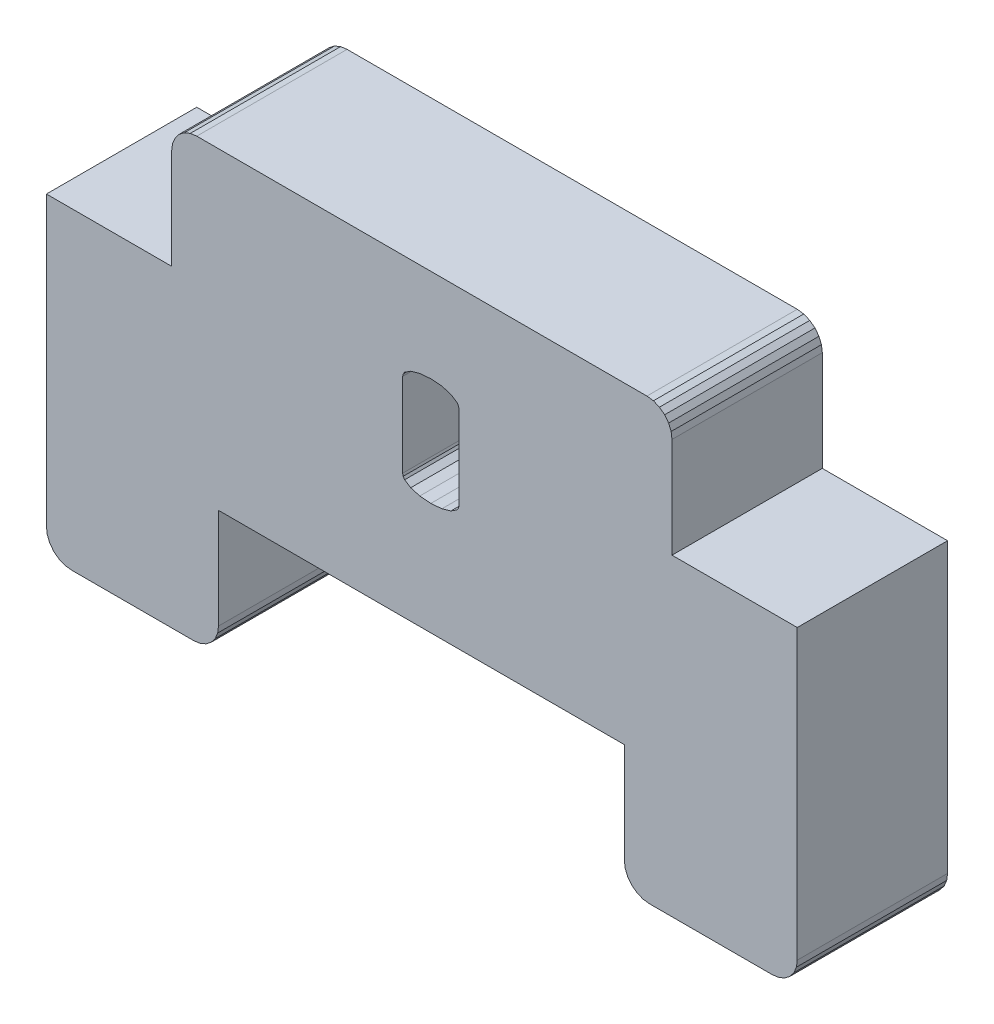
SolidWorks part; units mm, degrees
material "Maple"
ref_plane "Front Plane" through (0, 0, 0) normal (0, 0, 1) x (1, 0, 0)
ref_plane "Top Plane" through (0, 0, 0) normal (0, 1, 0) x (1, 0, 0)
ref_plane "Right Plane" through (0, 0, 0) normal (1, 0, 0) x (0, 0, -1)
sketch "Sketch1" plane through (0, 0, 0) normal (0, 0, 1) x (1, 0, 0)
  line L367 (-477.0213, -244.8724) -> (-477.2801, -244.9065)
  line L368 (-482.6801, -244.7725) -> (-482.439, -244.8724)
  line L369 (-482.8873, -244.6136) -> (-482.6801, -244.7725)
  line L370 (-483.0462, -244.4065) -> (-482.8873, -244.6136)
  line L371 (-499.3801, -243.9065) -> (-499.3801, -239.9065)
  line L372 (-476.2801, -243.9065) -> (-476.2801, -232.4065)
  line L373 (-483.1801, -243.9065) -> (-483.1461, -244.1653)
  line L374 (-476.3142, -244.1653) -> (-476.4141, -244.4065)
  line L375 (-476.4141, -244.4065) -> (-476.573, -244.6136)
  line L376 (-483.1801, -239.9065) -> (-483.1801, -243.9065)
  line L377 (-499.3801, -239.9065) -> (-483.1801, -239.9065)
  line L378 (-501.1146, -227.9065) -> (-500.9557, -227.6993)
  line L379 (-476.573, -244.6136) -> (-476.7801, -244.7725)
  line L380 (-481.7801, -227.5404) -> (-482.0213, -227.4405)
  line L381 (-482.439, -244.8724) -> (-482.1801, -244.9065)
  line L382 (-505.2486, -244.9065) -> (-505.5074, -244.8724)
  line L383 (-500.1213, -244.8724) -> (-500.3801, -244.9065)
  line L384 (-500.5074, -227.4405) -> (-500.2486, -227.4065)
  line L385 (-500.2486, -227.4065) -> (-482.2801, -227.4065)
  line L386 (-476.7801, -244.7725) -> (-477.0213, -244.8724)
  line L387 (-506.2486, -232.4065) -> (-506.2486, -243.9065)
  line L388 (-501.2486, -232.4065) -> (-506.2486, -232.4065)
  line L389 (-500.7486, -227.5404) -> (-500.5074, -227.4405)
  line L390 (-500.9557, -227.6993) -> (-500.7486, -227.5404)
  line L391 (-501.2145, -228.1476) -> (-501.1146, -227.9065)
  line L392 (-501.2486, -228.4065) -> (-501.2145, -228.1476)
  line L393 (-501.2486, -232.4065) -> (-501.2486, -228.4065)
  line L394 (-506.2145, -244.1653) -> (-506.2486, -243.9065)
  line L395 (-506.1146, -244.4065) -> (-506.2145, -244.1653)
  line L396 (-505.9557, -244.6136) -> (-506.1146, -244.4065)
  line L397 (-505.7486, -244.7725) -> (-505.9557, -244.6136)
  line L398 (-505.5074, -244.8724) -> (-505.7486, -244.7725)
  line L399 (-505.2486, -244.9065) -> (-500.3801, -244.9065)
  line L400 (-499.8801, -244.7725) -> (-500.1213, -244.8724)
  line L401 (-499.673, -244.6136) -> (-499.8801, -244.7725)
  line L402 (-499.5141, -244.4065) -> (-499.673, -244.6136)
  line L403 (-499.4142, -244.1653) -> (-499.5141, -244.4065)
  line L404 (-499.3801, -243.9065) -> (-499.4142, -244.1653)
  line L405 (-483.1461, -244.1653) -> (-483.0462, -244.4065)
  line L406 (-482.1801, -244.9065) -> (-477.2801, -244.9065)
  line L407 (-476.2801, -243.9065) -> (-476.3142, -244.1653)
  line L408 (-481.2801, -232.4065) -> (-476.2801, -232.4065)
  line L409 (-481.2801, -228.4065) -> (-481.2801, -232.4065)
  line L410 (-481.2801, -228.4065) -> (-481.3142, -228.1476)
  line L411 (-481.3142, -228.1476) -> (-481.4141, -227.9065)
  line L412 (-481.4141, -227.9065) -> (-481.573, -227.6993)
  line L413 (-481.573, -227.6993) -> (-481.7801, -227.5404)
  line L414 (-482.0213, -227.4405) -> (-482.2801, -227.4065)
  line L8617 (-492.0299, -234.9492) -> (-492.0098, -235.0454)
  line L8618 (-492.0098, -235.0454) -> (-491.9495, -235.1342)
  line L8619 (-491.9495, -235.1342) -> (-491.7083, -235.2895)
  line L8620 (-491.7083, -235.2895) -> (-491.3469, -235.3948)
  line L8621 (-491.3469, -235.3948) -> (-490.906, -235.43)
  line L8622 (-490.906, -235.43) -> (-490.465, -235.3948)
  line L8623 (-490.465, -235.3948) -> (-490.1036, -235.2895)
  line L8624 (-490.1036, -235.2895) -> (-489.8624, -235.1342)
  line L8625 (-489.8624, -235.1342) -> (-489.8021, -235.0454)
  line L8626 (-489.8021, -235.0454) -> (-489.7821, -234.9492)
  line L8627 (-489.7821, -234.9492) -> (-489.7821, -231.6024)
  line L8628 (-489.7821, -231.6024) -> (-489.8021, -231.5063)
  line L8629 (-489.8021, -231.5063) -> (-489.8624, -231.4175)
  line L8630 (-489.8624, -231.4175) -> (-490.1036, -231.2622)
  line L8631 (-490.1036, -231.2622) -> (-490.465, -231.1568)
  line L8632 (-490.465, -231.1568) -> (-490.906, -231.1216)
  line L8633 (-490.906, -231.1216) -> (-491.3469, -231.1568)
  line L8634 (-491.3469, -231.1568) -> (-491.7083, -231.2622)
  line L8635 (-491.7083, -231.2622) -> (-491.9495, -231.4175)
  line L8636 (-491.9495, -231.4175) -> (-492.0098, -231.5063)
  line L8637 (-492.0098, -231.5063) -> (-492.0299, -231.6024)
  line L8638 (-492.0299, -231.6024) -> (-492.0299, -234.9492)
  line L8639 (-489.7821, -234.9492) -> (-489.8021, -235.0454)
  line L8640 (-489.8021, -235.0454) -> (-489.8624, -235.1342)
  line L8641 (-489.8624, -235.1342) -> (-490.1036, -235.2895)
  line L8642 (-490.1036, -235.2895) -> (-490.465, -235.3948)
  line L8643 (-490.465, -235.3948) -> (-490.906, -235.43)
  line L8644 (-490.906, -235.43) -> (-491.3469, -235.3948)
  line L8645 (-491.3469, -235.3948) -> (-491.7083, -235.2895)
  line L8646 (-491.7083, -235.2895) -> (-491.9495, -235.1342)
  line L8647 (-491.9495, -235.1342) -> (-492.0098, -235.0454)
  line L8648 (-492.0098, -235.0454) -> (-492.0299, -234.9492)
  line L8649 (-492.0299, -234.9492) -> (-492.0299, -231.6024)
  line L8650 (-492.0299, -231.6024) -> (-492.0098, -231.5063)
  line L8651 (-492.0098, -231.5063) -> (-491.9495, -231.4175)
  line L8652 (-491.9495, -231.4175) -> (-491.7083, -231.2622)
  line L8653 (-491.7083, -231.2622) -> (-491.3469, -231.1568)
  line L8654 (-491.3469, -231.1568) -> (-490.906, -231.1216)
  line L8655 (-490.906, -231.1216) -> (-490.465, -231.1568)
  line L8656 (-490.465, -231.1568) -> (-490.1036, -231.2622)
  line L8657 (-490.1036, -231.2622) -> (-489.8624, -231.4175)
  line L8658 (-489.8624, -231.4175) -> (-489.8021, -231.5063)
  line L8659 (-489.8021, -231.5063) -> (-489.7821, -231.6024)
  line L8660 (-489.7821, -231.6024) -> (-489.7821, -234.9492)
  line L8661 (-490.7498, -234.8247) -> (-489.7883, -236.0424)
extrude "Boss-Extrude1" add sketch "Sketch1" along normal blind 6 contours L380 L414 L385 L384 L389 L390 L378 L391 L392 L393 L388 L387 L394 L395 L396 L397 L398 L382 L399 L383 L400 L401 L402 L403 L404 L371 L377 L376 L373 L405 L370 L369 L368 L381 L406 L367 L386 L379 L375 L374 L407 L372 L408 L409 L410 L411 L412 L413 L8638 L8637
